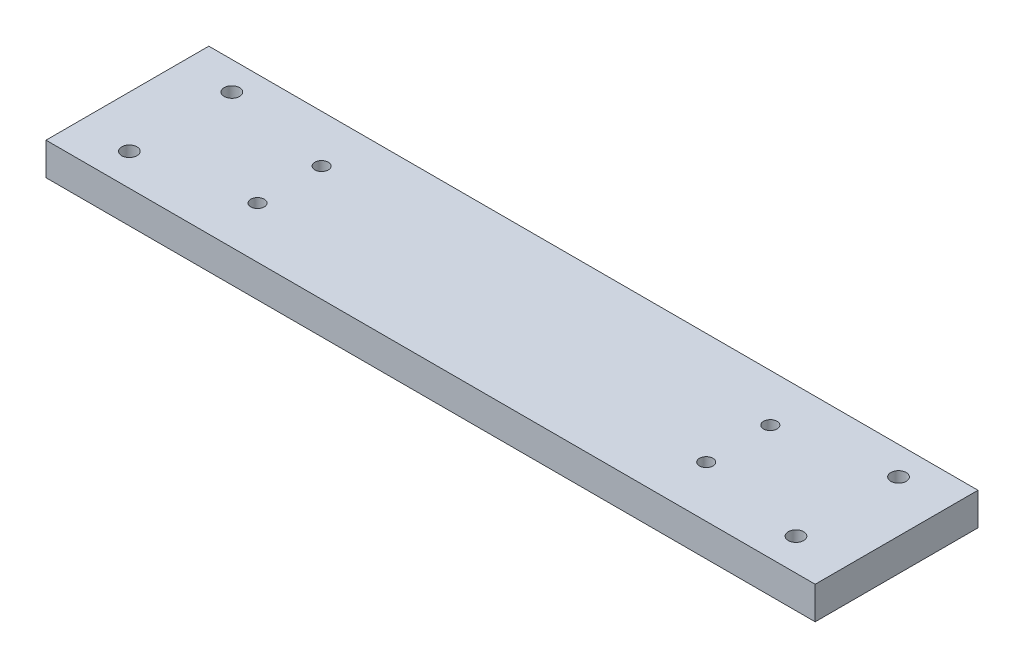
SolidWorks part; units mm, degrees
ref_plane "Front Plane" through (0, 0, 0) normal (0, 0, 1) x (1, 0, 0)
ref_plane "Top Plane" through (0, 0, 0) normal (0, 1, 0) x (1, 0, 0)
ref_plane "Right Plane" through (0, 0, 0) normal (1, 0, 0) x (0, 0, -1)
sketch "Sketch1" plane through (0, 0, 0) normal (0, 1, 0) x (1, 0, 0)
  line L1 (0, 0) -> (600, 0)
  line L2 (0, 0) -> (0, 127)
  line L3 (0, 127) -> (600, 127)
  line L4 (600, 0) -> (600, 127)
  dimension "D1" = 600
  dimension "D2" = 127
extrude "Boss-Extrude1" add sketch "Sketch1" along normal blind 25.4
sketch "Sketch2" plane through (0, 25.4, 0) normal (0, 1, 0) x (1, 0, 0)
  line L1 (0, 0) -> (300, 0)
  line L2 (0, 0) -> (0, 65)
  line L3 (0, 65) -> (300, 65)
  line L4 (300, 0) -> (300, 65)
  line L5 (40, 105) -> (560, 105)
  line L6 (40, 105) -> (40, 25)
  line L7 (40, 25) -> (560, 25)
  line L8 (560, 105) -> (560, 25)
  line L9 (40, 105) -> (560, 25) construction
  line L10 (40, 25) -> (560, 105) construction
  circle A0 centre (40, 105) radius 6
  circle A1 centre (40, 25) radius 6
  circle A2 centre (560, 25) radius 6
  circle A3 centre (560, 105) radius 6
  dimension "D1" = 300
  dimension "D2" = 65
  dimension "D3" = 520
  dimension "D4" = 80
extrude "Cut-Extrude1" cut sketch "Sketch2" against normal blind 25.4 contours A2 | A3 | A1 | A0
sketch "Sketch3" plane through (0, 25.4, 0) normal (0, 1, 0) x (1, 0, 0)
  line L1 (0, 0) -> (300, 0)
  line L2 (0, 0) -> (0, 65)
  line L3 (0, 65) -> (300, 65)
  line L4 (300, 0) -> (300, 65)
  line L5 (125, 90) -> (475, 90)
  line L6 (125, 90) -> (125, 40)
  line L7 (125, 40) -> (475, 40)
  line L8 (475, 90) -> (475, 40)
  line L9 (125, 90) -> (475, 40) construction
  line L10 (125, 40) -> (475, 90) construction
  circle A0 centre (125, 90) radius 5.25
  circle A1 centre (125, 40) radius 5.25
  circle A2 centre (475, 40) radius 5.25
  circle A3 centre (475, 90) radius 5.25
  dimension "D1" = 300
  dimension "D2" = 65
  dimension "D3" = 350
  dimension "D4" = 50
extrude "Cut-Extrude2" cut sketch "Sketch3" against normal blind 25.4 contours A0 | A1 | A2 | A3
